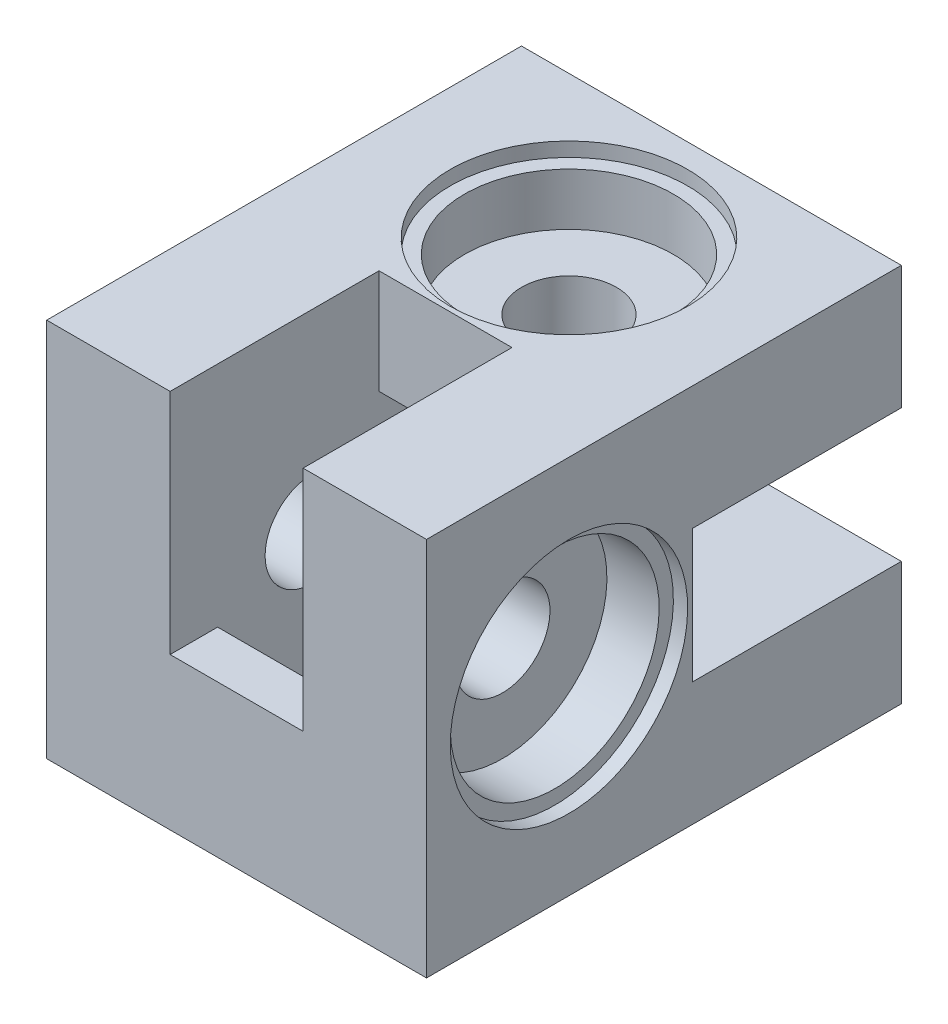
SolidWorks part; units mm, degrees
ref_plane "Plan de face" through (0, 0, 0) normal (0, 0, 1) x (1, 0, 0)
ref_plane "Plan de dessus" through (0, 0, 0) normal (0, 1, 0) x (1, 0, 0)
ref_plane "Plan de droite" through (0, 0, 0) normal (1, 0, 0) x (0, 0, -1)
sketch "Esquisse1" plane through (0, 0, 0) normal (0, 0, 1) x (1, 0, 0)
  line L1 (-40, 40) -> (0, 40)
  line L2 (-40, 40) -> (-40, 0)
  line L3 (-40, 0) -> (0, 0)
  line L4 (0, 40) -> (0, 0)
  dimension "D1" = 40
  dimension "D2" = 40
extrude "Boss.-Extru.1" add sketch "Esquisse1" along normal blind 50
sketch "Esquisse2" plane through (0, 40, 0) normal (0, 1, 0) x (1, 0, 0)
  line L0 (0, 0) -> (-40, 0) construction
  line L1 (-40, -50) -> (-40, 0) construction
  circle A0 centre (-20, -15) radius 5
  dimension "D1" = 10
  dimension "D2" = 15
  dimension "D3" = 20
extrude "Enlèv. mat.-Extru.1" cut sketch "Esquisse2" against normal through all
sketch "Esquisse3" plane through (-40, 0, 0) normal (-1, 0, 0) x (0, 0, 1)
  line L0 (50, 40) -> (50, 0) construction
  line L1 (50, 40) -> (0, 40) construction
  circle A0 centre (35, 20) radius 5
  dimension "D1" = 10
  dimension "D2" = 15
  dimension "D3" = 20
extrude "Enlèv. mat.-Extru.2" cut sketch "Esquisse3" against normal through all
sketch "Esquisse4" plane through (-40, 0, 0) normal (-1, 0, 0) x (0, 0, 1)
  line L1 (25, 27) -> (5, 27)
  line L2 (25, 27) -> (25, 13)
  line L3 (25, 13) -> (5, 13)
  line L4 (5, 27) -> (5, 13)
  line L5 (0, 40) -> (0, 0) construction
  line L6 (50, 0) -> (0, 0) construction
  line L7 (50, 40) -> (0, 40) construction
  dimension "D1" = 14
  dimension "D2" = 20
  dimension "D3" = 5
  dimension "D4" = 13
  dimension "D5" = 13
extrude "Enlèv. mat.-Extru.3" cut sketch "Esquisse4" against normal blind 29
sketch "Esquisse5" plane through (0, 0, 0) normal (0, -1, 0) x (1, 0, 0)
  line L0 (-40, 50) -> (0, 50) construction
  line L1 (-13, 25) -> (-27, 25)
  line L2 (-13, 25) -> (-13, 45)
  line L3 (-13, 45) -> (-27, 45)
  line L4 (-27, 25) -> (-27, 45)
  line L5 (-40, 50) -> (-40, 0) construction
  dimension "D1" = 20
  dimension "D2" = 5
  dimension "D3" = 14
  dimension "D4" = 13
extrude "Enlèv. mat.-Extru.4" cut sketch "Esquisse5" against normal blind 29
sketch "Esquisse6" plane through (0, 0, 0) normal (1, 0, 0) x (0, 0, -1)
  line L0 (0, 0) -> (0, 40) construction
  line L1 (0, 27) -> (-22, 27)
  line L2 (0, 27) -> (0, 13)
  line L3 (0, 13) -> (-22, 13)
  line L4 (-22, 27) -> (-22, 13)
  line L5 (-50, 0) -> (0, 0) construction
  dimension "D1" = 14
  dimension "D2" = 22
  dimension "D3" = 13
extrude "Enlèv. mat.-Extru.5" cut sketch "Esquisse6" against normal blind 24
sketch "Esquisse7" plane through (0, 40, 0) normal (0, 1, 0) x (1, 0, 0)
  line L0 (0, -50) -> (-40, -50) construction
  line L1 (-27, -50) -> (-13, -50)
  line L2 (-27, -50) -> (-27, -28)
  line L3 (-27, -28) -> (-13, -28)
  line L4 (-13, -50) -> (-13, -28)
  line L5 (-40, -50) -> (-40, 0) construction
  dimension "D1" = 14
  dimension "D2" = 22
  dimension "D3" = 13
extrude "Enlèv. mat.-Extru.6" cut sketch "Esquisse7" against normal blind 24
sketch "Esquisse8" plane through (0, 0, 0) normal (1, 0, 0) x (0, 0, -1)
  circle A0 centre (-35, 20) radius 11
  dimension "D1" = 22
extrude "Enlèv. mat.-Extru.7" cut sketch "Esquisse8" against normal blind 7
sketch "Esquisse9" plane through (0, 0, 0) normal (1, 0, 0) x (0, 0, -1)
  circle A0 centre (-35, 20) radius 12.5
  dimension "D1" = 25
extrude "Enlèv. mat.-Extru.8" cut sketch "Esquisse9" against normal blind 1.5
sketch "Esquisse10" plane through (0, 40, 0) normal (0, 1, 0) x (1, 0, 0)
  circle A0 centre (-20, -15) radius 11
  dimension "D1" = 22
extrude "Enlèv. mat.-Extru.9" cut sketch "Esquisse10" against normal blind 7
sketch "Esquisse11" plane through (0, 40, 0) normal (0, 1, 0) x (1, 0, 0)
  circle A0 centre (-20, -15) radius 12.5
  dimension "D1" = 25
extrude "Enlèv. mat.-Extru.10" cut sketch "Esquisse11" against normal blind 1.5
sketch "Esquisse12" plane through (0, 0, 0) normal (0, 0, -1) x (-1, 0, 0)
  line L0 (40, 12) -> (28, 12)
  line L1 (40, 40) -> (40, 0) construction
  line L2 (28, 12) -> (28, 0)
  line L3 (40, 0) -> (0, 0) construction
  line L4 (28, 0) -> (30, 0)
  line L5 (30, 0) -> (30, 10)
  line L6 (30, 10) -> (40, 10)
  line L7 (40, 10) -> (40, 12)
  dimension "D1" = 12
  dimension "D2" = 12
  dimension "D3" = 2
  dimension "D4" = 2
extrude "Boss.-Extru.2" add sketch "Esquisse12" along normal blind 20
